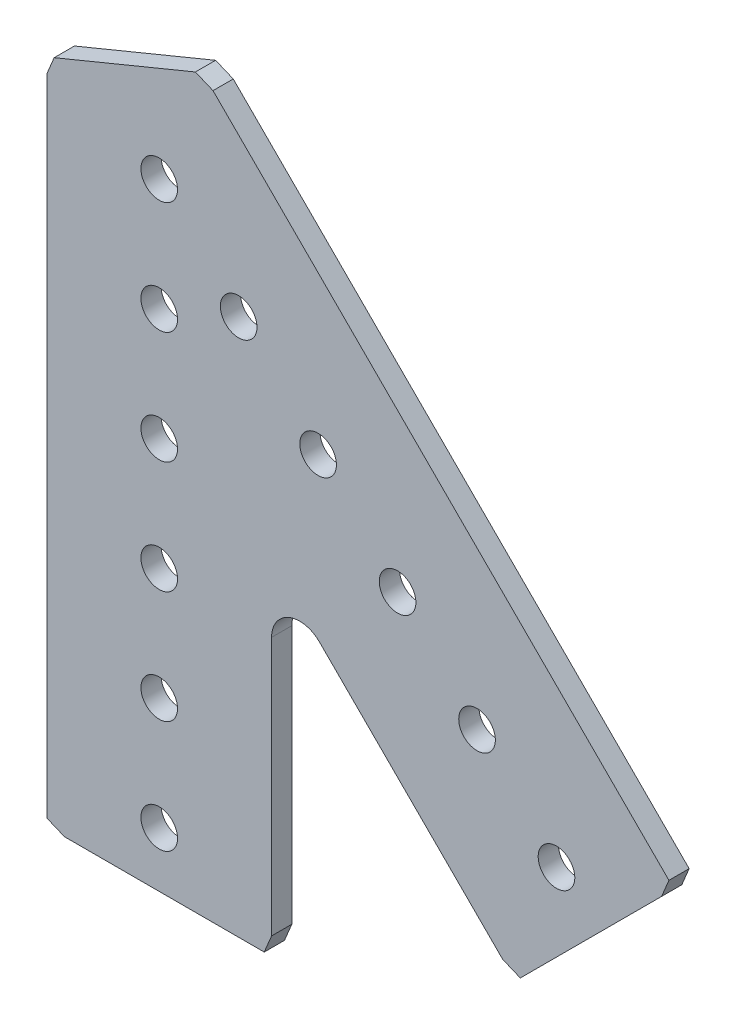
SolidWorks part; units mm, degrees
ref_plane "Front Plane" through (0, 0, 0) normal (0, 0, 1) x (1, 0, 0)
ref_plane "Top Plane" through (0, 0, 0) normal (0, 1, 0) x (1, 0, 0)
ref_plane "Right Plane" through (0, 0, 0) normal (1, 0, 0) x (0, 0, -1)
ref_plane "Plane1" through (0, 0, 2.286) normal (0, 0, 1) x (1, 0, 0)
sketch "Sketch1" plane through (0, 0, 2.286) normal (0, 0, 1) x (1, 0, 0)
  line L0 (-12.7, 3.9564) -> (-12.7, -68.8935)
  line L1 (-12.7, -68.8935) -> (-10.7067, -69.723)
  line L2 (-10.7067, -69.723) -> (11.8705, -69.723)
  line L3 (11.8705, -69.723) -> (12.7, -67.7297)
  line L4 (12.7, -67.7297) -> (12.7, -38.5052)
  line L5 (18.1201, -36.2602) -> (38.8202, -56.9603)
  line L6 (38.8202, -56.9603) -> (40.8135, -57.7897)
  line L7 (40.8135, -57.7897) -> (56.7807, -41.8225)
  line L8 (56.7807, -41.8225) -> (57.6101, -39.8292)
  line L9 (57.6101, -39.8292) -> (6.081, 11.6999)
  line L10 (6.081, 11.6999) -> (4.0877, 12.5294)
  line L11 (4.0877, 12.5294) -> (-11.8705, 5.9497)
  line L12 (-11.8705, 5.9497) -> (-12.7, 3.9564)
  arc A0 (12.7, -38.5052) -> (18.1201, -36.2602) centre (15.875, -38.5052) cw
  circle A1 centre (0, -63.5) radius 2.0701
  circle A2 centre (35.921, -35.921) radius 2.0701
  circle A3 centre (17.9605, -17.9605) radius 2.0701
  circle A4 centre (0, -38.1) radius 2.0701
  circle A5 centre (0, -12.7) radius 2.0701
  circle A6 centre (0, 0) radius 2.0701
  circle A7 centre (8.9803, -8.9803) radius 2.0701
  circle A8 centre (0, -25.4) radius 2.0701
  circle A9 centre (0, -50.8) radius 2.0701
  circle A10 centre (26.9408, -26.9408) radius 2.0701
  circle A11 centre (44.9013, -44.9013) radius 2.0701
extrude "Boss-Extrude1" add sketch "Sketch1" against normal blind 2.286
